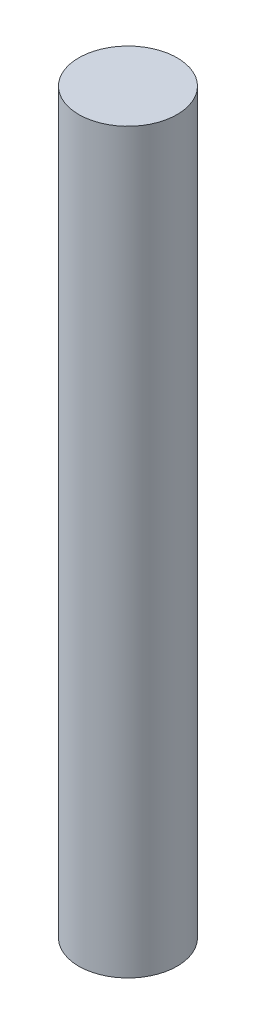
SolidWorks part; units mm, degrees
ref_plane "Спереди" through (0, 0, 0) normal (0, 0, 1) x (1, 0, 0)
ref_plane "Сверху" through (0, 0, 0) normal (0, 1, 0) x (1, 0, 0)
ref_plane "Справа" through (0, 0, 0) normal (1, 0, 0) x (0, 0, -1)
sketch "Эскиз1" plane through (0, 0, 0) normal (0, 1, 0) x (1, 0, 0)
  circle A0 centre (0, 0) radius 2
extrude "Бобышка-Вытянуть1" add sketch "Эскиз1" along normal blind 30
